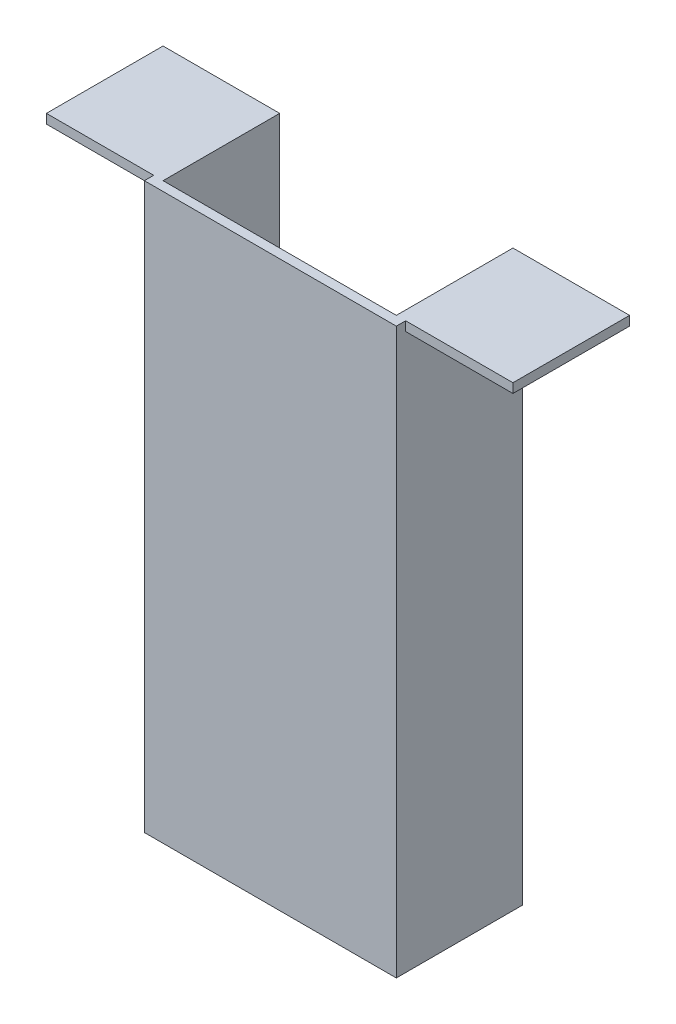
SolidWorks part; units mm, degrees
ref_plane "Front Plane" through (0, 0, 0) normal (0, 0, 1) x (1, 0, 0)
ref_plane "Top Plane" through (0, 0, 0) normal (0, 1, 0) x (1, 0, 0)
ref_plane "Right Plane" through (0, 0, 0) normal (1, 0, 0) x (0, 0, -1)
sketch "Sketch1" plane through (0, 0, 0) normal (0, 0, 1) x (1, 0, 0)
  line L0 (2.338, 2.1762) -> (2.338, 121.1762)
  line L1 (2.338, 2.1762) -> (52.338, 2.1762)
  line L2 (52.338, 2.1762) -> (52.338, 121.1762)
  line L3 (2.338, 121.1762) -> (-22.662, 121.1762)
  line L4 (52.338, 121.1762) -> (77.338, 121.1762)
  line L5 (-22.662, 121.1762) -> (-22.662, 119.1762)
  line L6 (-22.662, 119.1762) -> (0.338, 119.1762)
  line L7 (0.338, 119.1762) -> (0.338, 0.1762)
  line L8 (0.338, 0.1762) -> (54.338, 0.1762)
  line L9 (54.338, 0.1762) -> (54.338, 119.1762)
  line L10 (54.338, 119.1762) -> (77.338, 119.1762)
  line L11 (77.338, 119.1762) -> (77.338, 121.1762)
  dimension "D1" = 50
  dimension "D2" = 119
  dimension "D3" = 119
  dimension "D4" = 25
  dimension "D5" = 25
  dimension "D6" = 2
  dimension "D7" = 2
  dimension "D8" = 2
  dimension "D9" = 2
  dimension "D10" = 2
extrude "Boss-Extrude1" add sketch "Sketch1" along normal blind 25
sketch "Sketch3" plane through (0, 0, 25) normal (0, 0, 1) x (1, 0, 0)
  line L9 (77.338, 121.1762) -> (52.338, 121.1762) construction
  line L14 (0.338, 0.1762) -> (54.338, 0.1762)
  line L15 (0.338, 0.1762) -> (0.338, 121.1762)
  line L16 (0.338, 121.1762) -> (54.338, 121.1762)
  line L17 (54.338, 0.1762) -> (54.338, 121.1762)
  dimension "D1" = 54
extrude "Boss-Extrude2" add sketch "Sketch3" along normal blind 2
